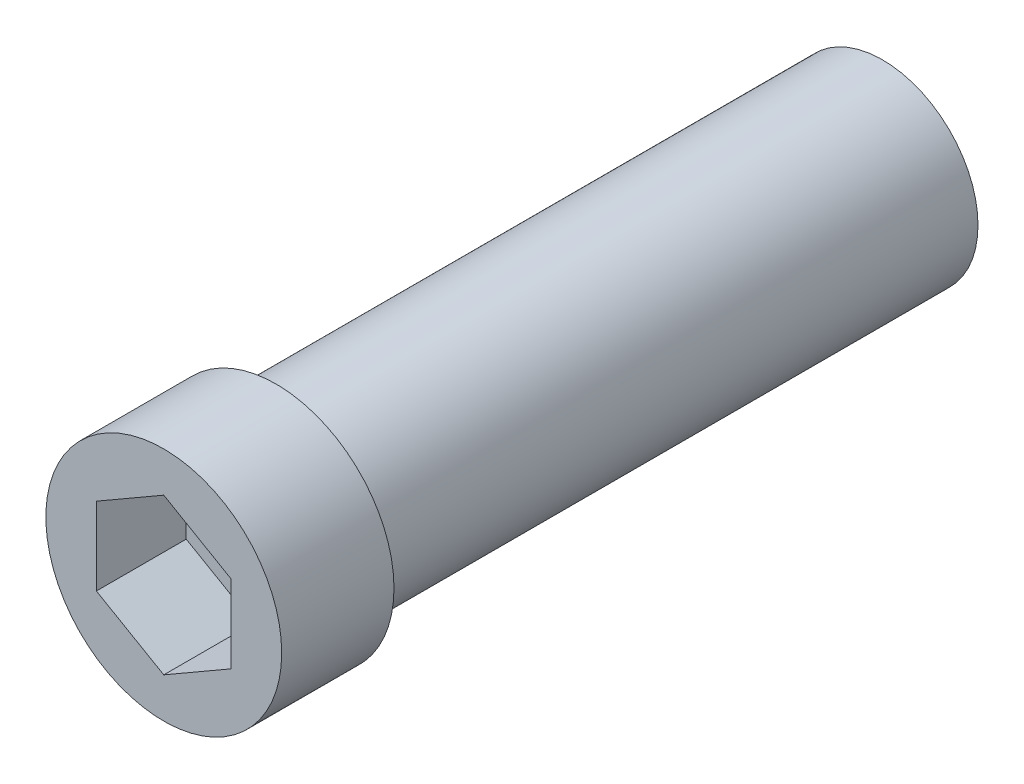
SolidWorks part; units mm, degrees
ref_plane "Front Plane" through (0, 0, 0) normal (0, 0, 1) x (1, 0, 0)
ref_plane "Top Plane" through (0, 0, 0) normal (0, 1, 0) x (1, 0, 0)
ref_plane "Right Plane" through (0, 0, 0) normal (1, 0, 0) x (0, 0, -1)
sketch "Sketch1" plane through (0, 0, 0) normal (0, 0, 1) x (1, 0, 0)
  circle A2 centre (0, 0) radius 4.25
extrude "Boss-Extrude1" add sketch "Sketch1" along normal blind 27
sketch "Sketch2" plane through (0, 0, 27) normal (0, 0, 1) x (1, 0, 0)
  circle A0 centre (0, 0) radius 5.25
extrude "Boss-Extrude2" add sketch "Sketch2" along normal blind 5
ref_plane "Plane1" through (4.25, 0, 0) normal (1, 0, 0) x (0, 0, -1)
sketch "Sketch7" plane through (0, 0, 32) normal (0, 0, 1) x (1, 0, 0)
  circle A0 centre (0, 0) radius 1.75
extrude "Cut-Extrude4" cut sketch "Sketch7" against normal through all
sketch "Sketch9" plane through (0, 0, 32) normal (0, 0, 1) x (1, 0, 0)
  line L1 (0, 3.4641) -> (-3, 1.7321)
  line L2 (-3, 1.7321) -> (-3, -1.7321)
  line L3 (-3, -1.7321) -> (0, -3.4641)
  line L4 (0, -3.4641) -> (3, -1.7321)
  line L5 (3, -1.7321) -> (3, 1.7321)
  line L6 (3, 1.7321) -> (0, 3.4641)
  circle A0 centre (0, 0) radius 3 construction
  dimension "D1" = 6
extrude "Cut-Extrude6" cut sketch "Sketch9" against normal blind 4
